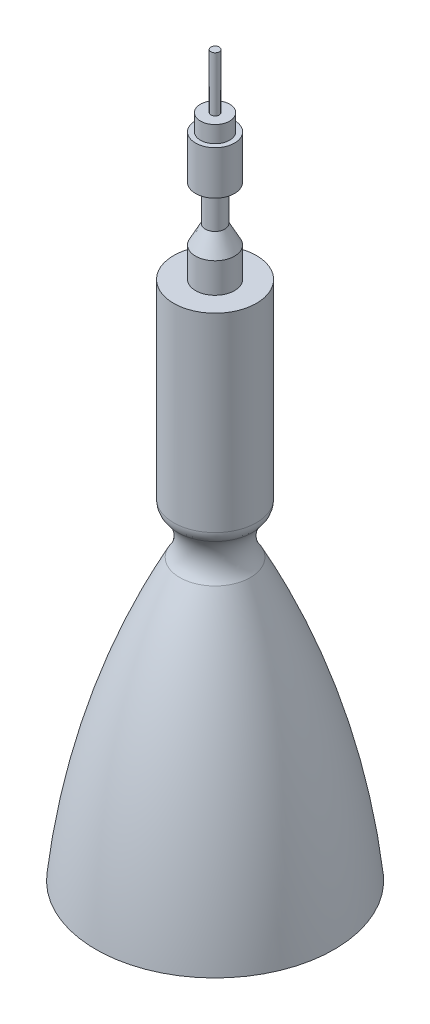
SolidWorks part; units mm, degrees
material "Custom Plastic"
ref_plane "Front Plane" through (0, 0, 0) normal (0, 0, 1) x (1, 0, 0)
ref_plane "Top Plane" through (0, 0, 0) normal (0, 1, 0) x (1, 0, 0)
ref_plane "Right Plane" through (0, 0, 0) normal (1, 0, 0) x (0, 0, -1)
sketch "Sketch1" plane through (0, 0, 0) normal (0, 0, 1) x (1, 0, 0)
  line L0 (0, 0) -> (76, 0)
  line L1 (0, 0) -> (0, 332)
  line L2 (26.4077, 206.4685) -> (26.4077, 332)
  line L3 (26.4077, 332) -> (0, 332)
  line L4 (0, 0) -> (0, 376.7255) construction
  arc A0 (76, 0) -> (22.5014, 178.6355) centre (-414.1882, -49.4752) ccw
  arc A1 (22.5014, 178.6355) -> (26.4077, 206.4685) centre (38.371, 190.5988) cw
  dimension "D1" = 76
  dimension "D2" = 332
revolve "Revolve1" add sketch "Sketch1" angle 360 about L4
fillet "Fillet1" radius 10 1 edges at (0, 206.4685, -26.4077)
sketch "Sketch2" plane through (0, 0, 0) normal (0, 0, 1) x (1, 0, 0)
  line L0 (0, 332) -> (0, 459)
  line L1 (26.4077, 332) -> (-26.4077, 332) construction
  line L2 (0, 332) -> (12.4299, 332)
  line L3 (12.4299, 332) -> (12.4299, 351.0712)
  line L4 (12.4299, 351.0712) -> (6.2149, 362.8504)
  line L5 (6.2149, 362.8504) -> (6.2149, 385.6236)
  line L6 (6.2149, 385.6236) -> (12.4299, 385.6236)
  line L7 (12.4299, 385.6236) -> (12.4299, 413.501)
  line L8 (12.4299, 413.501) -> (9.3224, 413.501)
  line L9 (9.3224, 413.501) -> (9.3224, 424.1023)
  line L10 (9.3224, 424.1023) -> (2.6648, 424.1023)
  line L11 (2.6648, 424.1023) -> (2.6648, 459)
  line L12 (2.6648, 459) -> (0, 459)
  line L13 (0, 332) -> (0, 489.4115) construction
  dimension "D1" = 127
revolve "Revolve2" add sketch "Sketch2" angle 360 about L13
